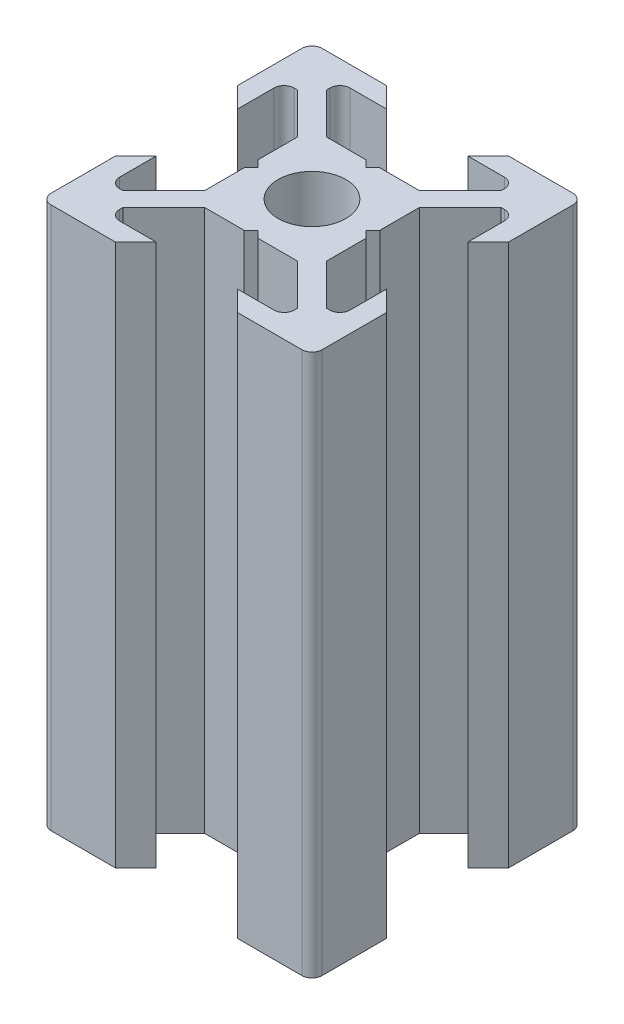
SolidWorks part; units mm, degrees
ref_plane "Face" through (0, 0, 0) normal (0, 0, 1) x (1, 0, 0)
ref_plane "Dessus" through (0, 0, 0) normal (0, 1, 0) x (1, 0, 0)
ref_plane "Droite" through (0, 0, 0) normal (1, 0, 0) x (0, 0, -1)
sketch "Esquisse1" plane through (0, 0, 0) normal (0, 1, 0) x (1, 0, 0)
  line L0 (0, 0) -> (0, 10) construction
  line L1 (0, 0) -> (-10, 0) construction
  line L2 (-10, 0) -> (-10, 10) construction
  line L3 (-10, 10) -> (0, 10) construction
  line L4 (0, 4) -> (-0.5, 4.5)
  line L5 (-0.5, 4.5) -> (-3.4393, 4.5)
  line L6 (-3.4393, 4.5) -> (-6.4393, 7.5)
  line L7 (-6.4393, 7.5) -> (-6.4393, 8.5)
  line L8 (-6.4393, 8.5) -> (-3, 8.5)
  line L9 (-3, 8.5) -> (-4.5, 10)
  line L10 (-4.5, 10) -> (-10, 10)
  line L11 (0, 0) -> (-10, 10) construction
  line L12 (-10, 4.5) -> (-10, 10)
  line L13 (-8.5, 3) -> (-10, 4.5)
  line L14 (-8.5, 6.4393) -> (-8.5, 3)
  line L15 (-7.5, 6.4393) -> (-8.5, 6.4393)
  line L16 (-4.5, 3.4393) -> (-7.5, 6.4393)
  line L17 (-4.5, 0.5) -> (-4.5, 3.4393)
  line L18 (-4, 0) -> (-4.5, 0.5)
  line L19 (0, -4) -> (-0.5, -4.5)
  line L20 (-0.5, -4.5) -> (-3.4393, -4.5)
  line L21 (-4, 0) -> (-4.5, -0.5)
  line L22 (-4.5, -0.5) -> (-4.5, -3.4393)
  line L23 (-4.5, -3.4393) -> (-7.5, -6.4393)
  line L24 (-3.4393, -4.5) -> (-6.4393, -7.5)
  line L25 (-3, -8.5) -> (-4.5, -10)
  line L26 (-6.4393, -8.5) -> (-3, -8.5)
  line L27 (-6.4393, -7.5) -> (-6.4393, -8.5)
  line L28 (-7.5, -6.4393) -> (-8.5, -6.4393)
  line L29 (-4.5, -10) -> (-10, -10)
  line L30 (-10, -4.5) -> (-10, -10)
  line L31 (-8.5, -3) -> (-10, -4.5)
  line L32 (-8.5, -6.4393) -> (-8.5, -3)
  line L33 (8.5, -6.4393) -> (8.5, -3)
  line L34 (8.5, -3) -> (10, -4.5)
  line L35 (10, -4.5) -> (10, -10)
  line L36 (4.5, -10) -> (10, -10)
  line L37 (7.5, -6.4393) -> (8.5, -6.4393)
  line L38 (6.4393, -7.5) -> (6.4393, -8.5)
  line L39 (6.4393, -8.5) -> (3, -8.5)
  line L40 (3, -8.5) -> (4.5, -10)
  line L41 (3.4393, -4.5) -> (6.4393, -7.5)
  line L42 (4.5, -3.4393) -> (7.5, -6.4393)
  line L43 (4.5, -0.5) -> (4.5, -3.4393)
  line L44 (4, 0) -> (4.5, -0.5)
  line L45 (0.5, -4.5) -> (3.4393, -4.5)
  line L46 (0, -4) -> (0.5, -4.5)
  line L47 (4, 0) -> (4.5, 0.5)
  line L48 (4.5, 0.5) -> (4.5, 3.4393)
  line L49 (4.5, 3.4393) -> (7.5, 6.4393)
  line L50 (7.5, 6.4393) -> (8.5, 6.4393)
  line L51 (8.5, 6.4393) -> (8.5, 3)
  line L52 (8.5, 3) -> (10, 4.5)
  line L53 (10, 4.5) -> (10, 10)
  line L54 (4.5, 10) -> (10, 10)
  line L55 (3, 8.5) -> (4.5, 10)
  line L56 (6.4393, 8.5) -> (3, 8.5)
  line L57 (6.4393, 7.5) -> (6.4393, 8.5)
  line L58 (3.4393, 4.5) -> (6.4393, 7.5)
  line L59 (0.5, 4.5) -> (3.4393, 4.5)
  line L60 (0, 4) -> (0.5, 4.5)
  circle A0 centre (0, 0) radius 2.5
  dimension "D10" = 5
  dimension "D1" = 10
  dimension "D2" = 45
  dimension "D3" = 45
  dimension "D4" = 1.5
  dimension "D5" = 7
  dimension "D6" = 1
  dimension "D7" = 4.5
  dimension "D8" = 0.5
  dimension "D9" = 0.75
extrude "Extrusion1" add sketch "Esquisse1" along normal blind 40
fillet "Congé1" radius 0.75 12 edges at (-8.5, 20, -6.4393) (-6.4393, 20, -8.5) (8.5, 20, -6.4393) (6.4393, 20, -8.5) (-8.5, 20, 6.4393) (-6.4393, 20, 8.5) (8.5, 20, 6.4393) (6.4393, 20, 8.5) (10, 20, -10) (-10, 20, -10) (-10, 20, 10) (10, 20, 10)
